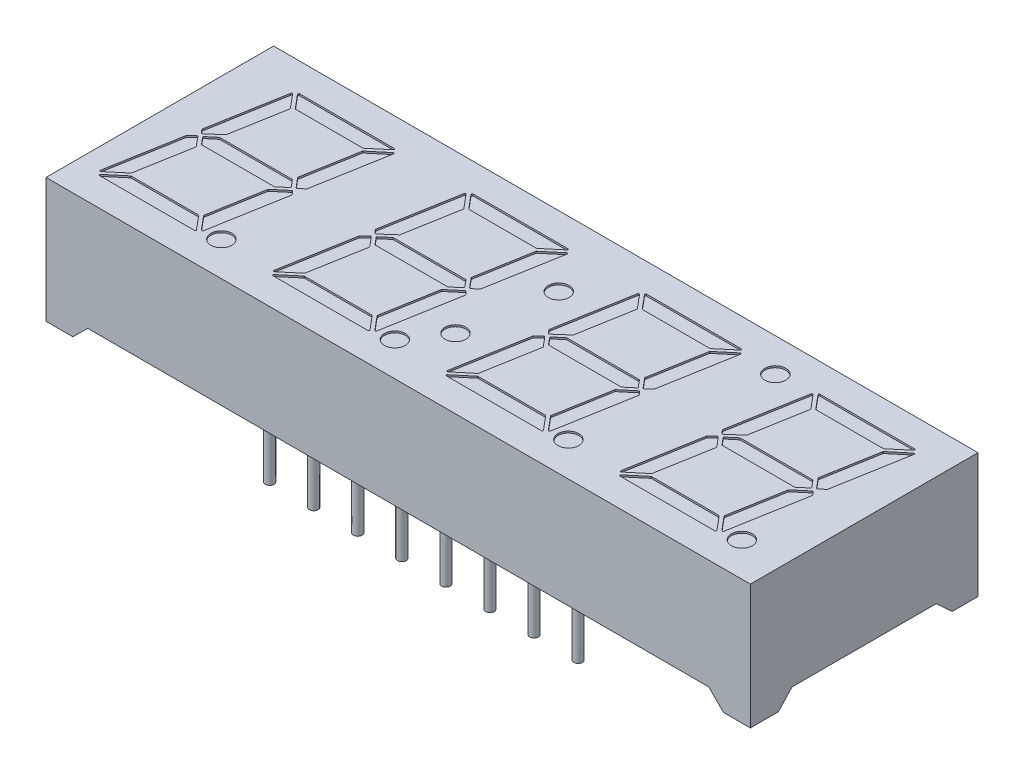
SolidWorks part; units mm, degrees
ref_plane "Front Plane" through (0, 0, 0) normal (0, 0, 1) x (1, 0, 0)
ref_plane "Top Plane" through (0, 0, 0) normal (0, 1, 0) x (1, 0, 0)
ref_plane "Right Plane" through (0, 0, 0) normal (1, 0, 0) x (0, 0, -1)
sketch "Sketch1" plane through (0, 0, 0) normal (0, 0, 1) x (1, 0, 0)
  line L1 (0, 0) -> (40.6, 0)
  line L2 (0, 0) -> (0, 7.1805)
  line L3 (0, 7.1805) -> (40.6, 7.1805)
  line L4 (40.6, 0) -> (40.6, 7.1805)
  dimension "D1" = 40.6
extrude "Boss-Extrude1" add sketch "Sketch1" against normal blind 13.12
sketch "Sketch2" plane through (0, 0, 0) normal (1, 0, 0) x (0, 0, -1)
  line L5 (13.12, 0) -> (0, 0) construction
  line L6 (2.4, 0.8472) -> (10.72, 0.8472)
  line L7 (2.4, 0.8472) -> (1.6127, 0)
  line L8 (10.72, 0.8472) -> (11.6317, 0)
  line L9 (11.6317, 0) -> (1.6127, 0)
extrude "Cut-Extrude1" cut sketch "Sketch2" against normal through all and the other way through all contours L9 L8 L6 L7
sketch "Sketch4" plane through (0, 0, 0) normal (0, 0, 1) x (1, 0, 0)
  line L5 (0, 0) -> (40.6, 0) construction
  line L6 (2.4, 0.85) -> (38.2, 0.85)
  line L7 (38.2, 0.85) -> (39.05, 0)
  line L8 (2.4, 0.85) -> (1.55, 0)
  line L9 (1.55, 0) -> (39.05, 0)
extrude "Cut-Extrude2" cut sketch "Sketch4" against normal through all
ref_plane "Plane1" through (0, 0.85, 0) normal (0, -1, 0) x (-1, 0, 0)
sketch "Sketch5" plane through (0, 0.85, 0) normal (0, -1, 0) x (-1, 0, 0)
  circle A0 centre (-19.03, 1.48) radius 0.25
  circle A1 centre (-16.49, 1.48) radius 0.25
  circle A2 centre (-13.95, 1.48) radius 0.25
  circle A3 centre (-11.41, 1.48) radius 0.25
  circle A4 centre (-19.03, 1.48) radius 0.25
  circle A5 centre (-16.49, 1.48) radius 0.25
  circle A6 centre (-13.95, 1.48) radius 0.25
  circle A7 centre (-21.57, 1.48) radius 0.25
  circle A8 centre (-19.03, 1.48) radius 0.25
  circle A9 centre (-16.49, 1.48) radius 0.25
  circle A10 centre (-24.11, 1.48) radius 0.25
  circle A11 centre (-21.57, 1.48) radius 0.25
  circle A12 centre (-19.03, 1.48) radius 0.25
  circle A13 centre (-26.65, 1.48) radius 0.25
  circle A14 centre (-24.11, 1.48) radius 0.25
  circle A15 centre (-21.57, 1.48) radius 0.25
  circle A16 centre (-21.57, 1.48) radius 0.25
  circle A17 centre (-24.11, 1.48) radius 0.25
  circle A18 centre (-26.65, 1.48) radius 0.25
  circle A19 centre (-29.19, 1.48) radius 0.25
  dimension "D1" = 4
  dimension "D2" = 5
extrude "Boss-Extrude2" add sketch "Sketch5" along normal blind 3.9 contours A3 | A1 | A0 | A7 | A10 | A13 | A19 | A2
ref_plane "Plane2" through (0, 0, -6.56) normal (0, 0, 1) x (1, 0, 0)
mirror "Mirror1" about plane through (0, 0, -6.56) normal (0, 0, 1) of "Boss-Extrude2"
ref_plane "Plane3" through (0, 7.1805, 0) normal (0, 1, 0) x (1, 0, 0)
sketch "Sketch6" plane through (0, 7.1805, 0) normal (0, 1, 0) x (1, 0, 0)
  line L0 (7.247, 7.2603) -> (7.7507, 6.66)
  line L1 (2.2964, 6.66) -> (3.0594, 7.3306)
  line L4 (6.9914, 5.8104) -> (7.7655, 6.46)
  line L5 (2.8692, 11.356) -> (2.0838, 6.9019)
  line L6 (1.9454, 6.1168) -> (1.1823, 1.7892)
  line L7 (2.2964, 6.46) -> (2.8001, 5.8597)
  line L8 (3.6129, 10.4696) -> (3.0594, 7.3306)
  line L9 (2.8001, 5.8597) -> (2.2386, 2.6755)
  line L10 (3.0267, 11.484) -> (8.7362, 11.484)
  line L11 (8.8649, 11.3314) -> (8.0916, 6.946)
  line L13 (3.7661, 10.5977) -> (7.6799, 10.5977)
  line L14 (6.9914, 5.8104) -> (6.4343, 2.6508)
  line L15 (1.3109, 1.636) -> (7.0248, 1.636)
  line L16 (2.3672, 2.5223) -> (6.2811, 2.5223)
  line L17 (2.8692, 11.356) -> (3.6129, 10.4696)
  line L18 (3.0267, 11.484) -> (3.7661, 10.5977)
  line L19 (7.9642, 6.2233) -> (7.178, 1.7645)
  line L20 (1.1823, 1.7892) -> (2.2386, 2.6755)
  line L21 (7.247, 7.2603) -> (7.8086, 10.4451)
  line L22 (7.6799, 10.5977) -> (8.7362, 11.484)
  line L23 (1.3109, 1.636) -> (2.3672, 2.5223)
  line L24 (6.2811, 2.5223) -> (7.0248, 1.636)
  line L25 (6.4343, 2.6508) -> (7.178, 1.7645)
  line L28 (7.8086, 10.4451) -> (8.8649, 11.3314)
  line L43 (7.5736, 6.56) -> (7.2017, 7.0032)
  line L46 (7.5736, 6.56) -> (7.0454, 6.1168)
  line L47 (2.8454, 6.1168) -> (7.0454, 6.1168)
  line L49 (3.0017, 7.0032) -> (7.2017, 7.0032)
  line L56 (2.4736, 6.56) -> (3.0017, 7.0032)
  line L63 (2.4736, 6.56) -> (2.8454, 6.1168)
  line L68 (2.2964, 6.46) -> (1.9454, 6.1168)
  line L70 (7.7655, 6.46) -> (7.9642, 6.2233)
  line L74 (2.2964, 6.66) -> (2.0838, 6.9019)
  line L78 (7.7507, 6.66) -> (8.0916, 6.946)
  circle A0 centre (8.14, 1.97) radius 0.6
extrude "Cut-Extrude3" cut sketch "Sketch6" against normal blind 0.1
fillet "Fillet1" radius 0.05 34 edges at (7.7655, 7.1305, -6.46) (3.0017, 7.1305, -7.0032) (2.2964, 7.1305, -6.66) (7.0248, 7.1305, -1.636) (6.2811, 7.1305, -2.5223) (1.3109, 7.1305, -1.636) (1.1823, 7.1305, -1.7892) (2.2386, 7.1305, -2.6755) (7.178, 7.1305, -1.7645) (6.4343, 7.1305, -2.6508) (2.3672, 7.1305, -2.5223) (6.9914, 7.1305, -5.8104) (7.247, 7.1305, -7.2603) (7.7507, 7.1305, -6.66) (7.0454, 7.1305, -6.1168) (2.8001, 7.1305, -5.8597) (2.2964, 7.1305, -6.46) (2.8454, 7.1305, -6.1168) (1.9454, 7.1305, -6.1168) (2.0838, 7.1305, -6.9019) (2.4736, 7.1305, -6.56) (7.2017, 7.1305, -7.0032) (7.9642, 7.1305, -6.2233) (8.0916, 7.1305, -6.946) (7.5736, 7.1305, -6.56) (3.0594, 7.1305, -7.3306) (3.6129, 7.1305, -10.4696) (3.7661, 7.1305, -10.5977) (7.6799, 7.1305, -10.5977) (7.8086, 7.1305, -10.4451) (8.8649, 7.1305, -11.3314) (8.7362, 7.1305, -11.484) (3.0267, 7.1305, -11.484) (2.8692, 7.1305, -11.356)
pattern_linear "LPattern1" count 4 spacing 10 along (1, 0, 0) of "Cut-Extrude3", "Fillet1"
sketch "Sketch7" plane through (0, 7.1805, 0) normal (0, 1, 0) x (1, 0, 0)
  circle A0 centre (20.4686, 9.084) radius 0.6
  circle A1 centre (19.5764, 4.024) radius 0.6
  circle A4 centre (30.841, 11.1961) radius 0.6
extrude "Cut-Extrude4" cut sketch "Sketch7" against normal blind 0.1
